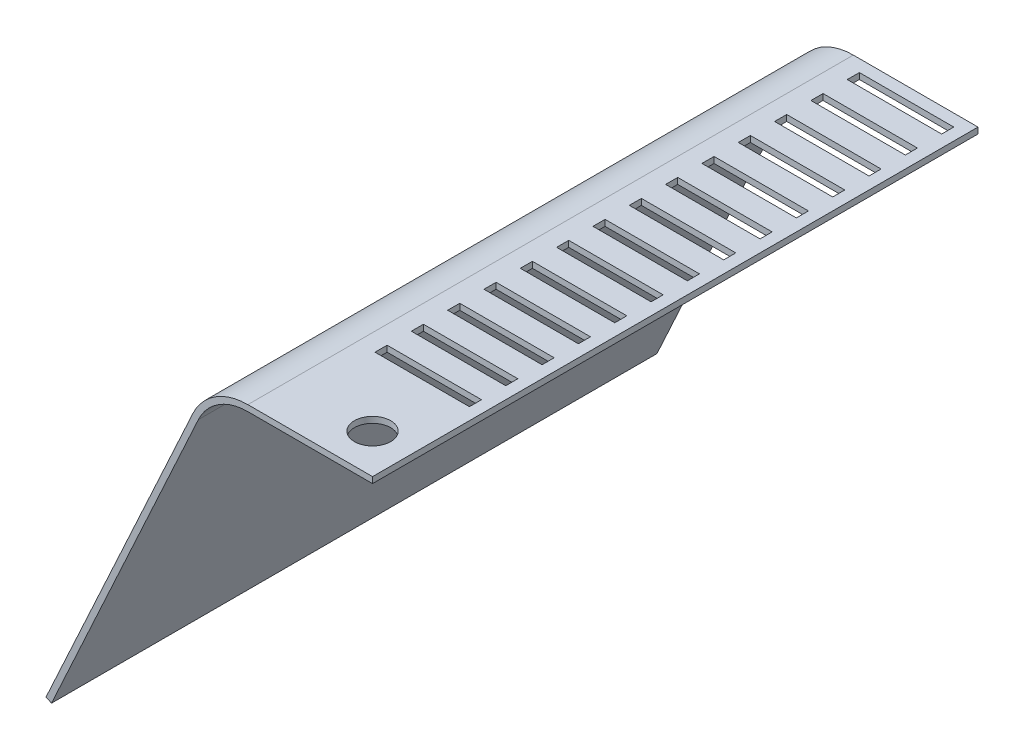
SolidWorks part; units mm, degrees
ref_plane "Front Plane" through (0, 0, 0) normal (0, 0, 1) x (1, 0, 0)
ref_plane "Top Plane" through (0, 0, 0) normal (0, 1, 0) x (1, 0, 0)
ref_plane "Right Plane" through (0, 0, 0) normal (1, 0, 0) x (0, 0, -1)
sketch "Sketch1" plane through (0, 0, 0) normal (0, 0, 1) x (1, 0, 0)
  line L0 (0, 0) -> (-205.95, 0)
  line L1 (-296.7862, -58.1816) -> (-539.333, -585.0317)
  arc A0 (-205.95, 0) -> (-296.7862, -58.1816) centre (-205.95, -100) ccw
  point P3 (-123.0219, -115.7602)
  point P5 (-74.041, 0)
  point P6 (-303.6689, 0)
  point P7 (-586.5218, -445.0954)
  dimension "D1" = 100
  dimension "D2" = 205.95
  dimension "D3" = 114.72
  dimension "D4" = 580
extrude "Extrude-Thin1" add sketch "Sketch1" along normal mid plane 1000 thin thin type one direction reverse wall 10
sketch "Sketch2" plane through (0, 0, 0) normal (0, 1, 0) x (1, 0, 0)
  line L0 (0, -500) -> (0, 500) construction
  line L1 (-175.95, 480) -> (-20, 480)
  line L2 (-175.95, 480) -> (-175.95, 460)
  line L3 (-175.95, 460) -> (-20, 460)
  line L4 (-20, 480) -> (-20, 460)
  line L5 (0, 500) -> (-205.95, 500) construction
  line L6 (-205.95, -500) -> (-205.95, 500) construction
  dimension "D1" = 20
  dimension "D2" = 20
  dimension "D3" = 20
  dimension "D4" = 30
extrude "Cut-Extrude1" cut sketch "Sketch2" against normal through all
pattern_linear "LPattern1" count 14 spacing 60 along (0, 0, 1) of "Cut-Extrude1"
sketch "Sketch3" plane through (0, 0, 0) normal (0, 1, 0) x (1, 0, 0)
  line L0 (0, -500) -> (0, 500) construction
  line L1 (0, -500) -> (-205.95, -500) construction
  circle A0 centre (-65, -435) radius 30
  dimension "D1" = 65
  dimension "D2" = 65
  dimension "D3" = 60
extrude "Cut-Extrude2" cut sketch "Sketch3" against normal through all
